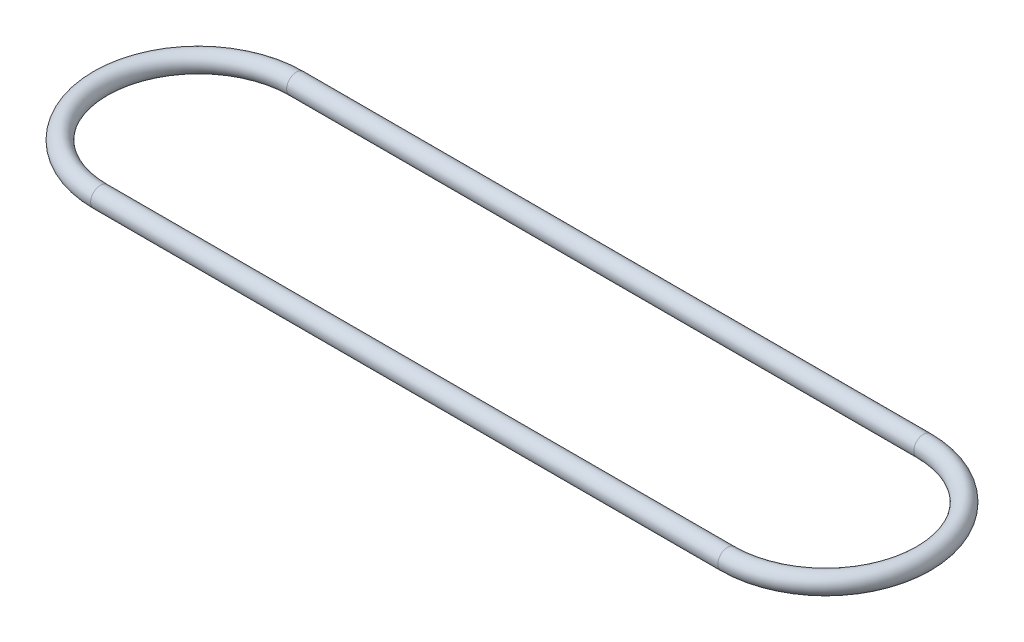
SolidWorks part; units mm, degrees
ref_plane "Front" through (0, 0, 0) normal (0, 0, 1) x (1, 0, 0)
ref_plane "Top" through (0, 0, 0) normal (0, 1, 0) x (1, 0, 0)
ref_plane "Right" through (0, 0, 0) normal (1, 0, 0) x (0, 0, -1)
sketch "Sketch1" plane through (0, 0, 0) normal (0, 1, 0) x (1, 0, 0)
  line L0 (0, 31.75) -> (203.2, 31.75)
  line L1 (203.2, -31.75) -> (0, -31.75)
  arc A0 (0, 31.75) -> (0, -31.75) centre (0, 0) ccw
  arc A1 (203.2, -31.75) -> (203.2, 31.75) centre (203.2, 0) ccw
  dimension "D1" = 63.5
  dimension "D2" = 203.2
sketch "Sketch2" plane through (0, 0, 0) normal (1, 0, 0) x (0, 0, -1)
  circle A0 centre (-31.75, 0) radius 3.175
  dimension "D1" = 6.35
sweep "Sweep1" add profiles "Sketch2" path "Sketch1"
sketch "Sketch3" plane through (0, 0, 0) normal (0, 1, 0) x (1, 0, 0)
  circle A0 centre (0, 0) radius 6.35 construction
  circle A1 centre (203.2, 0) radius 6.35 construction
